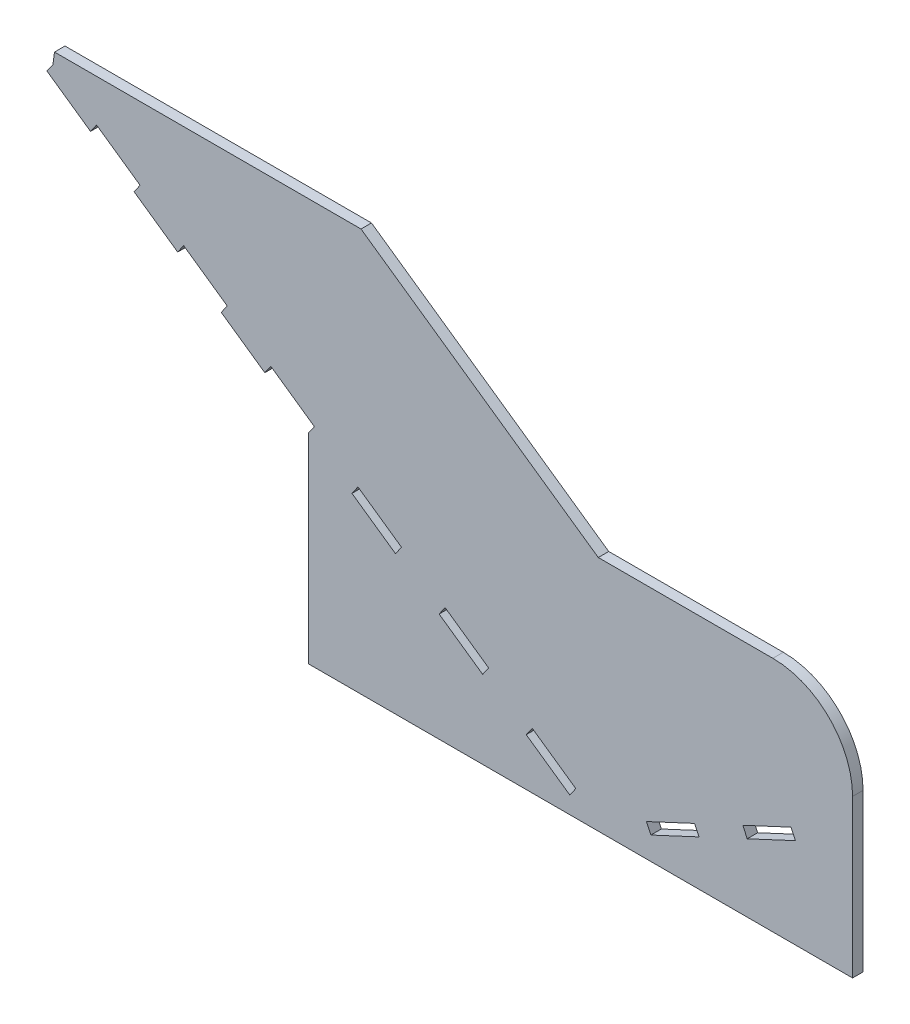
SolidWorks part; units mm, degrees
ref_plane "Front Plane" through (0, 0, 0) normal (0, 0, 1) x (1, 0, 0)
ref_plane "Top Plane" through (0, 0, 0) normal (0, 1, 0) x (1, 0, 0)
ref_plane "Right Plane" through (0, 0, 0) normal (1, 0, 0) x (0, 0, -1)
sketch "Sketch1" plane through (0, 0, 0) normal (0, 0, 1) x (1, 0, 0)
  line L0 (-266.1228, 202.268) -> (26.7318, 202.268)
  line L1 (26.7318, 202.268) -> (253.4396, 43.7785)
  line L2 (253.4396, 43.7785) -> (253.4396, -173.1615)
  line L3 (253.4396, -173.1615) -> (-267.6237, 191.1096)
  line L4 (-23.5449, 8.2747) -> (-23.5449, -173.1615)
  line L5 (-23.5449, -173.1615) -> (253.4396, -173.1615)
  line L6 (-267.6237, 191.1096) -> (-283.5851, 202.268)
  line L7 (-266.1228, 202.268) -> (-283.5851, 202.268)
  line L8 (-267.6237, 191.1096) -> (-273.3533, 182.9138)
  line L9 (-273.3533, 182.9138) -> (-231.7186, 153.8072)
  line L10 (-231.7186, 153.8072) -> (-225.9889, 162.0031)
  line L11 (-184.3542, 132.8966) -> (-190.0838, 124.7007)
  line L12 (-190.0838, 124.7007) -> (-148.4491, 95.5942)
  line L13 (-148.4491, 95.5942) -> (-142.7195, 103.79)
  line L14 (-101.0847, 74.6835) -> (-106.8144, 66.4877)
  line L15 (-106.8144, 66.4877) -> (-65.1796, 37.3812)
  line L16 (-65.1796, 37.3812) -> (-59.45, 45.577)
  line L17 (-17.8153, 16.4705) -> (-23.5449, 8.2747)
  line L18 (-23.5449, 8.2747) -> (18.0899, -20.8318)
  line L19 (18.0899, -20.8318) -> (23.8195, -12.636)
  line L20 (65.4542, -41.7425) -> (59.7246, -49.9383)
  line L21 (59.7246, -49.9383) -> (101.3593, -79.0448)
  line L22 (101.3593, -79.0448) -> (107.089, -70.849)
  line L23 (148.7237, -99.9555) -> (142.9941, -108.1513)
  line L24 (142.9941, -108.1513) -> (184.6288, -137.2578)
  line L25 (184.6288, -137.2578) -> (190.3584, -129.062)
  line L26 (231.9932, -158.1685) -> (226.2635, -166.3643)
  line L27 (-266.1228, 202.268) -> (-267.6237, 191.1096)
  line L28 (267.8983, -195.4708) -> (273.6279, -187.275)
  line L29 (18.0899, -20.8318) -> (59.7246, -49.9383)
  line L30 (101.3593, -79.0448) -> (142.9941, -108.1513)
  line L31 (184.6288, -137.2578) -> (226.2635, -166.3643)
  line L32 (253.4396, 43.7785) -> (420.249, 43.7785)
  line L33 (253.4396, 43.7785) -> (253.4396, -173.1615)
  line L34 (253.4396, -173.1615) -> (496.449, -173.1615)
  line L35 (496.449, -32.4215) -> (496.449, -173.1615)
  line L36 (-270.4885, 187.0117) -> (-283.5851, 349.1746) construction
  line L37 (299.48, -151.6925) -> (303.7062, -160.7556)
  line L46 (253.4396, -173.1615) -> (496.449, -59.8444)
  line L47 (303.7062, -160.7556) -> (349.7466, -139.2866)
  line L48 (349.7466, -139.2866) -> (345.5205, -130.2235)
  line L49 (391.5609, -108.7545) -> (437.6013, -87.2855)
  line L50 (391.5609, -108.7545) -> (395.7871, -117.8176)
  line L51 (437.6013, -87.2855) -> (441.8275, -96.3486)
  line L52 (395.7871, -117.8176) -> (441.8275, -96.3486)
  line L54 (496.449, -173.1615) -> (-23.5449, -173.1615)
  line L55 (496.449, -173.1615) -> (496.449, -182.6865)
  line L56 (496.449, -182.6865) -> (-23.5449, -182.6865)
  line L57 (-23.5449, -173.1615) -> (-23.5449, -182.6865)
  arc A0 (420.249, 43.7785) -> (496.449, -32.4215) centre (420.249, -32.4215) cw
  circle A1 centre (486.1274, -130.2235) radius 41.275 construction
  dimension "D27" = 76.2
  dimension "D34" = 82.55
  dimension "D1" = 177.8
  dimension "D2" = 10
  dimension "D3" = 50.8
  dimension "D4" = 10
  dimension "D5" = 50.8
  dimension "D6" = 50.8
  dimension "D7" = 19.475
  dimension "D8" = 17.4623
  dimension "D9" = 50.8
  dimension "D10" = 50.8
  dimension "D11" = 10
  dimension "D12" = 50.8
  dimension "D13" = 50.8
  dimension "D14" = 292.8546
  dimension "D15" = 276.6141
  dimension "D16" = 10
  dimension "D17" = 10
  dimension "D18" = 50.8
  dimension "D19" = 216.94
  dimension "D20" = 10
  dimension "D21" = 50.8
  dimension "D22" = 50.8
  dimension "D23" = 25
  dimension "D24" = 50.8
  dimension "D25" = 50.8
  dimension "D26" = 243.0094
  dimension "D28" = 50.8
  dimension "D29" = 50.8
  dimension "D30" = 10
  dimension "D31" = 10
  dimension "D32" = 50.8
  dimension "D33" = 50.8
  dimension "D35" = 9.525
extrude "Boss-Extrude1" add sketch "Sketch1" along normal blind 10
